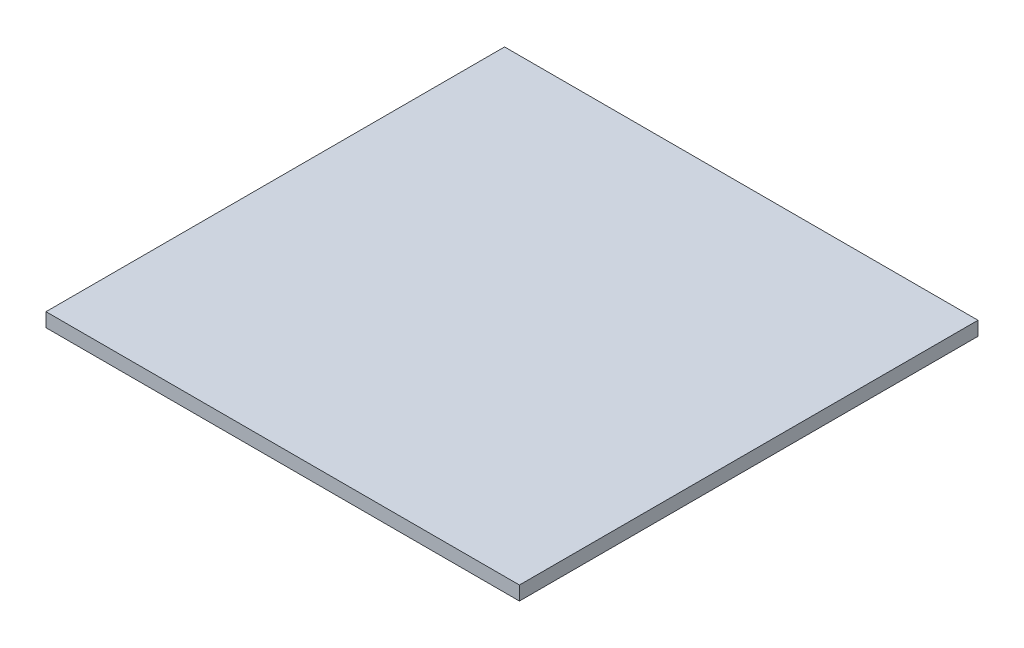
SolidWorks part; units mm, degrees
ref_plane "Front Plane" through (0, 0, 0) normal (0, 0, 1) x (1, 0, 0)
ref_plane "Top Plane" through (0, 0, 0) normal (0, 1, 0) x (1, 0, 0)
ref_plane "Right Plane" through (0, 0, 0) normal (1, 0, 0) x (0, 0, -1)
sketch "Sketch1" plane through (0, 0, 0) normal (0, 1, 0) x (1, 0, 0)
  line L1 (-44.2815, 20.698) -> (57.7185, 20.698)
  line L2 (-44.2815, 20.698) -> (-44.2815, -78.102)
  line L3 (-44.2815, -78.102) -> (57.7185, -78.102)
  line L4 (57.7185, 20.698) -> (57.7185, -78.102)
  dimension "D1" = 102
  dimension "D2" = 98.8
extrude "Boss-Extrude1" add sketch "Sketch1" along normal blind 3
equation "\"Fit\"= 1"
equation "\"cover width\"= 98.8"
equation "\"bottom 1 length\" = 102"
equation "\"thinner acrylic\"= 3"
equation "\"D1@Sketch1\"=\"bottom 1 length\""
equation "\"D2@Sketch1\"=\"cover width\""
equation "\"D1@Boss-Extrude1\"=\"thinner acrylic\""
